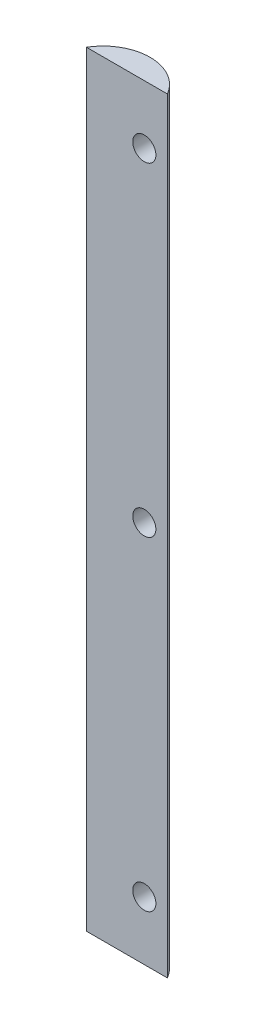
SolidWorks part; units mm, degrees
ref_plane "Front Plane" through (0, 0, 0) normal (0, 0, 1) x (1, 0, 0)
ref_plane "Top Plane" through (0, 0, 0) normal (0, 1, 0) x (1, 0, 0)
ref_plane "Right Plane" through (0, 0, 0) normal (1, 0, 0) x (0, 0, -1)
sketch "Sketch2" plane through (0, 0, 0) normal (0, 1, 0) x (1, 0, 0)
  line L2 (0, 0) -> (6.35, 0)
  line L3 (0, 0) -> (-15.875, 0)
  arc A2 (-15.875, 0) -> (6.35, 0) centre (-4.7625, -6.5484) cw
  point P4 (0, 0)
  point P7 (-4.7625, 6.35)
  dimension "D1" = 6.35
  dimension "D2" = 15.875
  dimension "D3" = 6.35
extrude "Boss-Extrude1" add sketch "Sketch2" along normal blind 209.9724 from offset 6.35 offset against normal yes
sketch "Sketch1" plane through (0, 0, 0) normal (0, 0, 1) x (1, 0, 0)
  line L0 (0, -6.35) -> (0, 203.6224) construction
  line L1 (-15.875, -6.35) -> (6.35, -6.35) construction
  line L2 (-15.875, 203.6224) -> (6.35, 203.6224) construction
  circle A1 centre (0, 187.5363) radius 3.175
  circle A2 centre (0, 9.7361) radius 3.175
  circle A3 centre (0, 98.6362) radius 3.175
  dimension "D1" = 6.35
  dimension "D3" = 16.0861
  dimension "D2" = 16.0861
extrude "Cut-Extrude2" cut sketch "Sketch1" against normal through all both
